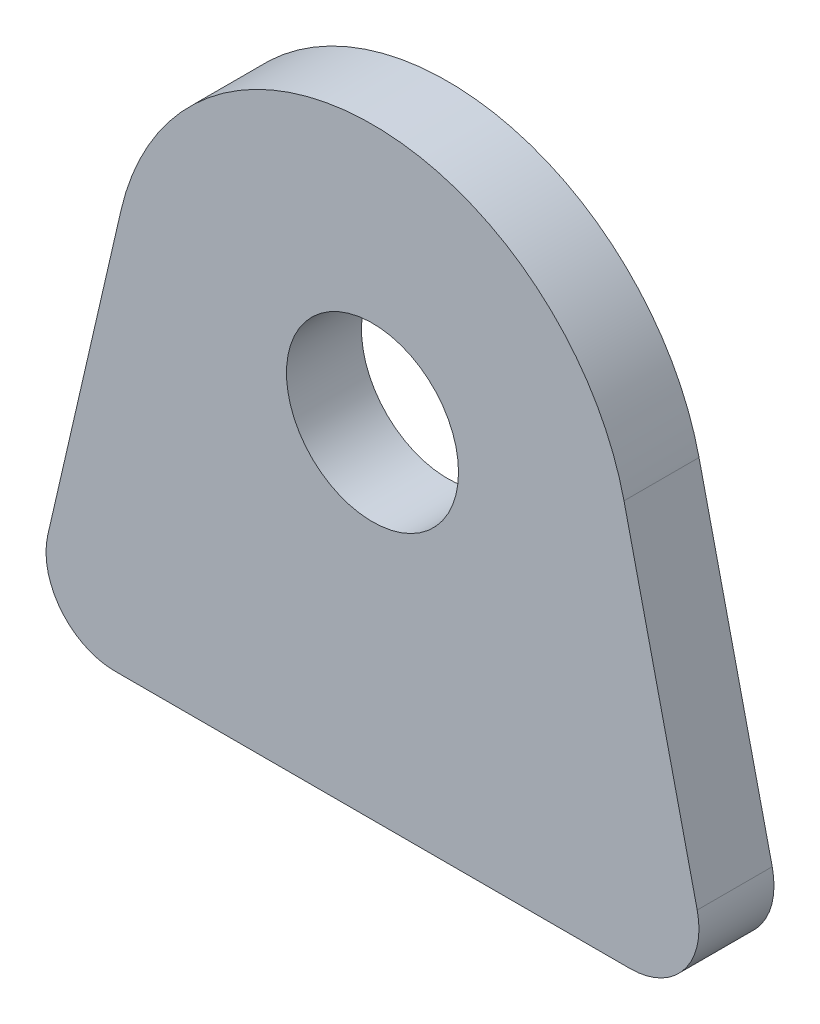
SolidWorks part; units mm, degrees
ref_plane "Front" through (0, 0, 0) normal (0, 0, 1) x (1, 0, 0)
ref_plane "Top" through (0, 0, 0) normal (0, 1, 0) x (1, 0, 0)
ref_plane "Right" through (0, 0, 0) normal (1, 0, 0) x (0, 0, -1)
sketch "Sketch1" plane through (0, 0, 0) normal (0, 0, 1) x (1, 0, 0)
  line L0 (0, 0) -> (0, 12.7) construction
  line L2 (-9.2819, 14.8382) -> (-11.9835, 3.1102)
  line L3 (-9.5084, 0) -> (9.5084, 0)
  line L4 (9.2819, 14.8382) -> (11.9835, 3.1102)
  circle A0 centre (0, 12.7) radius 3.175
  arc A1 (9.2819, 14.8382) -> (-9.2819, 14.8382) centre (0, 12.7) ccw
  arc A2 (-11.9835, 3.1102) -> (-9.5084, 0) centre (-9.5084, 2.54) ccw
  arc A3 (9.5084, 0) -> (11.9835, 3.1102) centre (9.5084, 2.54) ccw
  point P8 (-12.7, 0)
  point P13 (12.7, 0)
  dimension "D2" = 6.35
  dimension "D4" = 9.525
  dimension "D5" = 2.54
  dimension "D1" = 25.4
  dimension "D3" = 12.7
extrude "Boss-Extrude1" add sketch "Sketch1" along normal mid plane 2.7686
